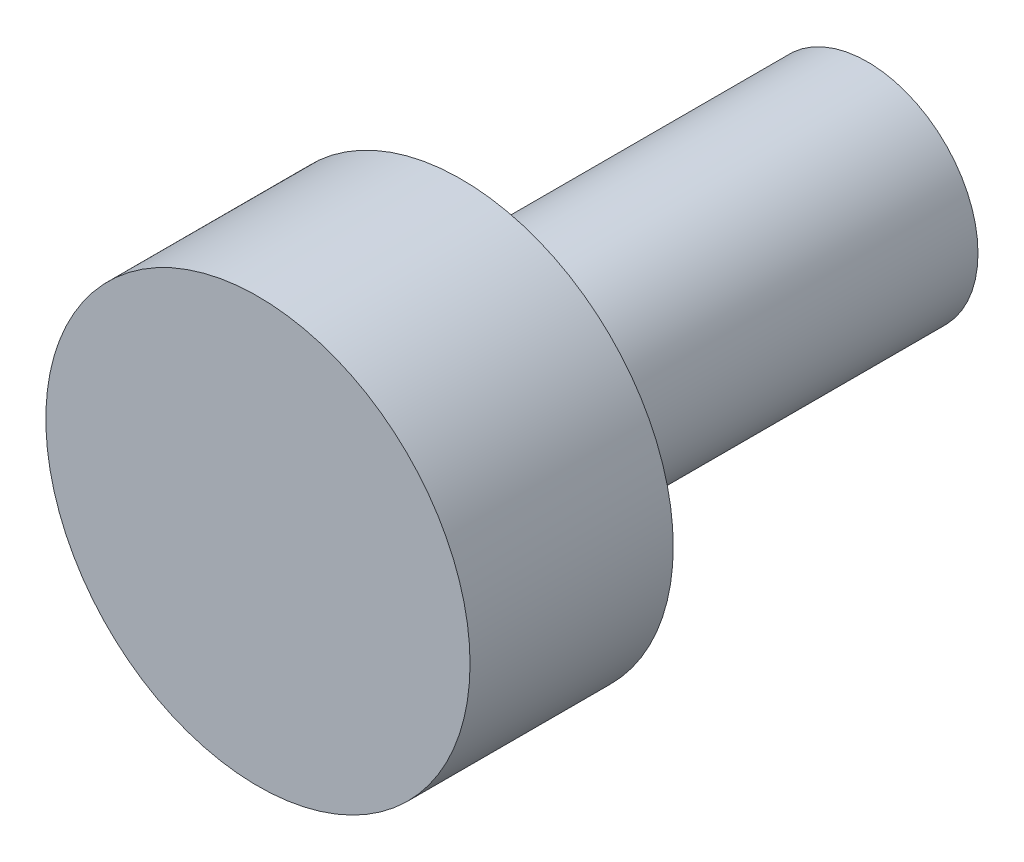
SolidWorks part; units mm, degrees
ref_plane "Front Plane" through (0, 0, 0) normal (0, 0, 1) x (1, 0, 0)
ref_plane "Top Plane" through (0, 0, 0) normal (0, 1, 0) x (1, 0, 0)
ref_plane "Right Plane" through (0, 0, 0) normal (1, 0, 0) x (0, 0, -1)
sketch "Sketch1" plane through (0, 0, 0) normal (0, 0, 1) x (1, 0, 0)
  circle A0 centre (0, 0) radius 1.7272
  dimension "D1" = 3.4544
extrude "Boss-Extrude1" add sketch "Sketch1" along normal blind 6.35
sketch "Sketch2" plane through (0, 0, 6.35) normal (0, 0, 1) x (1, 0, 0)
  circle A0 centre (0, 0) radius 3.3147
  dimension "D1" = 6.6294
extrude "Boss-Extrude2" add sketch "Sketch2" along normal blind 3.175 contours A0
